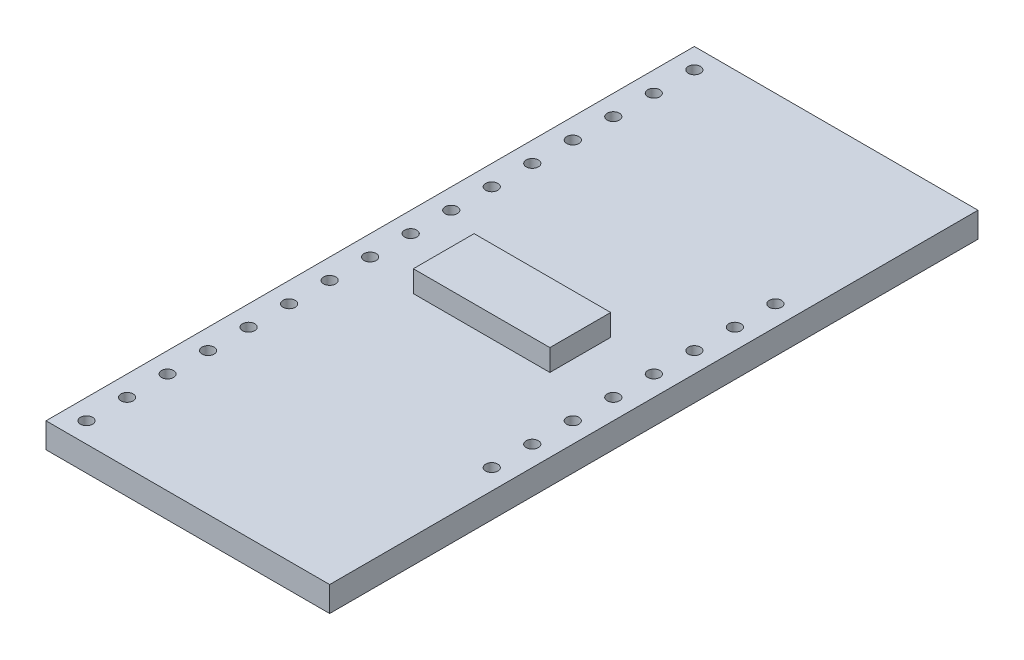
SolidWorks part; units mm, degrees
ref_plane "Front Plane" through (0, 0, 0) normal (0, 0, 1) x (1, 0, 0)
ref_plane "Top Plane" through (0, 0, 0) normal (0, 1, 0) x (1, 0, 0)
ref_plane "Right Plane" through (0, 0, 0) normal (1, 0, 0) x (0, 0, -1)
sketch "Sketch1" plane through (0, 0, 0) normal (0, 1, 0) x (1, 0, 0)
  line L1 (0, 0) -> (17.78, 0)
  line L2 (0, 0) -> (0, 40.64)
  line L3 (0, 40.64) -> (17.78, 40.64)
  line L4 (17.78, 0) -> (17.78, 40.64)
  dimension "D1" = 17.78
  dimension "D2" = 40.64
extrude "PCB" add sketch "Sketch1" along normal blind 1.5748
sketch "Sketch2" plane through (0, 1.5748, 0) normal (0, 1, 0) x (1, 0, 0)
  circle A0 centre (1.27, 1.27) radius 0.381
extrude "Hole Pattern seed 1" cut sketch "Sketch2" against normal blind 1.5748
pattern_linear "HP 1x16" count 16 spacing 2.54 along (0, 0, -1) of "Hole Pattern seed 1"
sketch "Sketch3" plane through (0, 1.5748, 0) normal (0, 1, 0) x (1, 0, 0)
  circle A0 centre (16.51, 11.43) radius 0.381
extrude "Hole Pattern seed 2" cut sketch "Sketch3" against normal blind 1.5748
pattern_linear "HP 1x08" count 8 spacing 2.54 along (0, 0, -1) of "Hole Pattern seed 2"
sketch "Sketch4" plane through (0, 1.5748, 0) normal (0, 1, 0) x (1, 0, 0)
  line L1 (4.6101, 18.415) -> (13.1699, 18.415)
  line L2 (4.6101, 18.415) -> (4.6101, 22.225)
  line L3 (4.6101, 22.225) -> (13.1699, 22.225)
  line L4 (13.1699, 18.415) -> (13.1699, 22.225)
  line L5 (4.6101, 18.415) -> (13.1699, 22.225) construction
  line L6 (4.6101, 22.225) -> (13.1699, 18.415) construction
  point P0 (8.89, 20.32)
  dimension "D1" = 3.81
  dimension "D2" = 8.5598
extrude "SSOP-24" add sketch "Sketch4" along normal blind 1.3513
